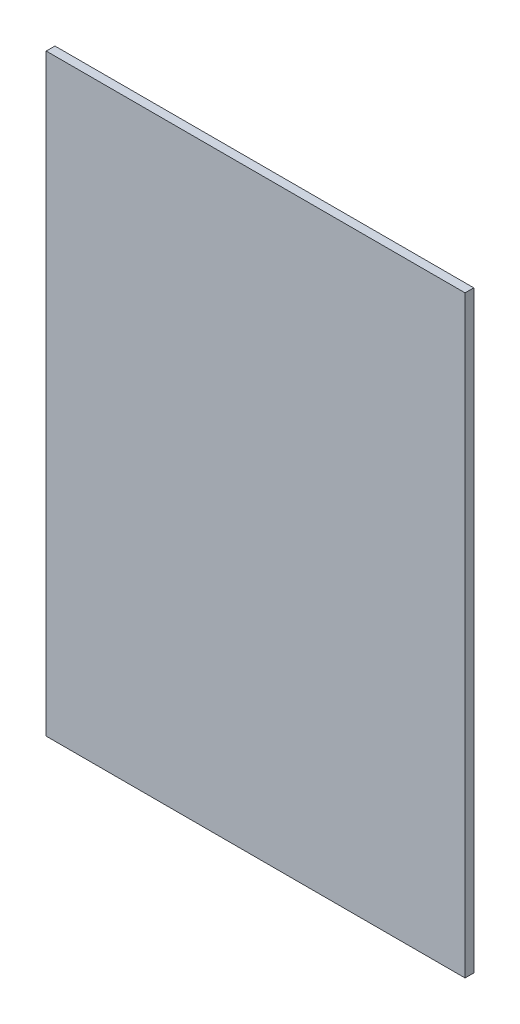
SolidWorks part; units mm, degrees
ref_plane "Plan de face" through (0, 0, 0) normal (0, 0, 1) x (1, 0, 0)
ref_plane "Plan de dessus" through (0, 0, 0) normal (0, 1, 0) x (1, 0, 0)
ref_plane "Plan de droite" through (0, 0, 0) normal (1, 0, 0) x (0, 0, -1)
sketch "Esquisse1" plane through (0, 0, 0) normal (0, 0, 1) x (1, 0, 0)
  line L1 (-290, 340) -> (190, 340)
  line L2 (-290, 340) -> (-290, -340)
  line L3 (-290, -340) -> (190, -340)
  line L4 (190, 340) -> (190, -340)
  dimension "D1" = 480
  dimension "D2" = 680
  dimension "D3" = 340
  dimension "D4" = 190
extrude "Boss.-Extru.1" add sketch "Esquisse1" along normal blind 10
